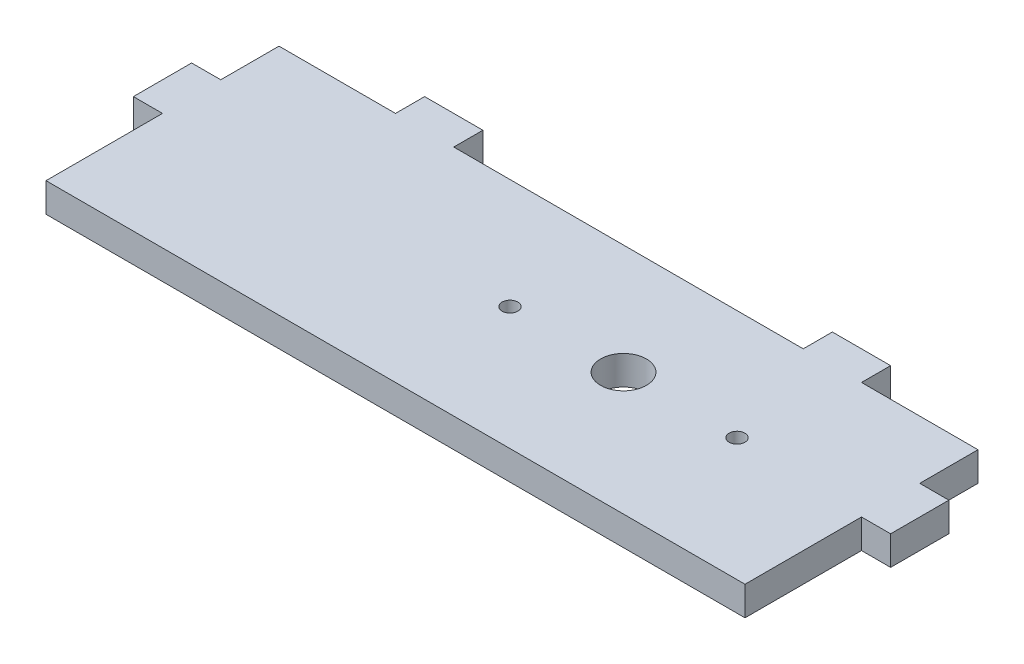
SolidWorks part; units mm, degrees
material "Beech"
ref_plane "Front Plane" through (0, 0, 0) normal (0, 0, 1) x (1, 0, 0)
ref_plane "Top Plane" through (0, 0, 0) normal (0, 1, 0) x (1, 0, 0)
ref_plane "Right Plane" through (0, 0, 0) normal (1, 0, 0) x (0, 0, -1)
sketch "Sketch1" plane through (0, 0, 0) normal (0, 1, 0) x (1, 0, 0)
  line L0 (0, 0) -> (0, 50.8)
  line L1 (0, 0) -> (152.4, 0)
  line L2 (0, 50.8) -> (152.4, 50.8)
  line L3 (152.4, 0) -> (152.4, 50.8)
  line L4 (0, 38.1) -> (-6.35, 38.1)
  line L5 (0, 38.1) -> (0, 25.4)
  line L6 (-6.35, 38.1) -> (-6.35, 25.4)
  line L7 (0, 25.4) -> (-6.35, 25.4)
  line L8 (25.4, 50.8) -> (25.4, 57.15)
  line L9 (25.4, 50.8) -> (38.1, 50.8)
  line L10 (25.4, 57.15) -> (38.1, 57.15)
  line L11 (38.1, 50.8) -> (38.1, 57.15)
  line L12 (114.3, 50.8) -> (114.3, 57.15)
  line L13 (114.3, 50.8) -> (127, 50.8)
  line L14 (114.3, 57.15) -> (127, 57.15)
  line L15 (127, 50.8) -> (127, 57.15)
  line L16 (152.4, 38.1) -> (158.75, 38.1)
  line L17 (152.4, 38.1) -> (152.4, 25.4)
  line L18 (158.75, 38.1) -> (158.75, 25.4)
  line L19 (152.4, 25.4) -> (158.75, 25.4)
  circle A0 centre (99.11, 26.8) radius 5
  circle A1 centre (123.86, 26.8) radius 1.725
  circle A2 centre (74.36, 26.8) radius 1.725
  point P27 (76.2, 50.8)
  dimension "D8" = 10
  dimension "D9" = 3.45
  dimension "D1" = 152.4
  dimension "D2" = 50.8
  dimension "D3" = 12.7
  dimension "D4" = 6.35
  dimension "D5" = 25.4
  dimension "D6" = 25.4
  dimension "D7" = 12.7
  dimension "D10" = 24.75
  dimension "D11" = 24.75
  dimension "D12" = 24
  dimension "D13" = 22.91
extrude "Boss-Extrude1" add sketch "Sketch1" along normal blind 6.35 contours L1 L3 L2 L0 A2 A1 A0 | L2 L11 L10 L8 | L7 L0 L4 L6 | L3 L19 L18 L16 | L2 L15 L14 L12
equation "\"CageLeftBottomEdge\"=22.11mm"
equation "\"CageLeftTopEdge\"=22.11mm"
equation "\"CageRightBottomEdge\"=21.63mm"
equation "\"CageRightTopEdge\"=21.63mm"
equation "\"CageHeight\"=86.04mm"
equation "\"CageLength\"=73.76mm"
equation "\"CageTopScrewClearance\"=10mm"
equation "\"CageBottomScrewClearance\"=25mm"
equation "\"CageLeftTopDepth\"= 11.65mm"
equation "\"CageLeftBottomDepth\"=11.11mm"
equation "\"CageLeftTopHeight\"=8.56175mm"
equation "\"CageLeftBottomHeight\"=16mm"
equation "\"CageRightTopDepth\"= 11.05mm"
equation "\"CageRightBottomDepth\"=10.58mm"
equation "\"CageRightTopHeight\"=9.6mm"
equation "\"CageRightBottomHeight\"=15.49mm"
equation "\"CageLeftTopChannelDepth\"=2.41908mm"
equation "\"CageLeftBottomChannelDepth\"=2.588mm"
equation "\"CageLeftChannelHeight\"=11.7mm"
equation "\"CageRightTopChannelDepth\"=2.32mm"
equation "\"CageRightBottomChannelDepth\"=2.318mm"
equation "\"CageRightChannelHeight\"=10mm"
equation "\"CageChanRelHeight\"=23.99mm"
equation "\"CageChanRelDepth\"=5.492mm"
equation "\"CageChamberRadius\"=16.261mm"
equation "\"CageScrewDiameter\"=4.8mm"
equation "\"CageSetScrewDiameter\"=3.5mm"
equation "\"CageAxleRadius\"=6.639mm"
equation "\"CageAxleKeyHeight\"=1.619mm"
equation "\"CageAxleKeyWidth\"=2.662mm"
equation "\"CageHoseWindowWidth\"=16.29mm"
equation "\"CageHoseWindowHeight\"=26.5mm"
equation "\"CageHoseWindow-Edge\"=8.89mm"
equation "\"CageScrew-VerticalEdge\"=5.0mm"
equation "\"CageScrew-HorizontalEdge\"=7.5mm"
equation "\"CageScrew-HoseCornerScrewEdge\"=4.45mm"
equation "\"CageAxle-BottomEdge\"=56.05mm"
equation "\"CageAxle-FrontEdge\"=46.03mm"
equation "\"CageBackSetScrew-Axle\"=40mm"
equation "\"CageFrontSetScrew-Axle\"=22mm"
equation "\"CageVelocityWindow-BackEdge\"=34.8mm"
equation "\"CageVelocityWindow-BottomEdge\"=27.55mm"
equation "\"CageVelocityWindowHeight\"=22.29mm"
equation "\"CageVelocityWindowWidth\"=12.61mm"
equation "\"TriggerSlot-BottomEdge\"=6.35mm"
equation "\"TriggerSlot-FrontEdge\"=15mm"
equation "\"TriggerSlotSize\"=6.7mm"
equation "\"TriggerRackOffset\"=.236224in"
equation "\"TriggerSlotSizeInt\"=.25in"
equation "\"MotorMountLegLength\"=.25in"
equation "\"GearOffset\"=.264907in"
equation "\"TriggerSlotSpacing\"=.25in"
equation "\"TriggerMiniSlotWidth\"=3.5mm"
equation "\"TriggerRackWidth\"=6.5mm"
equation "\"TGMGearFaceDiameter\"=24.40mm"
equation "\"TGMCylinderLength\"=15.00mm"
equation "\"TGMScrewHole-Center\"=8.70mm"
equation "\"TGMScrewHoleDiameter\"=5.04mm"
equation "\"TGMCenterHoleDiameter\"=9.50mm"
equation "\"TGMShaftCollarSideLength\"=19.00mm"
equation "\"TGMShaftCollarDockingDepth\"=7.00mm"
equation "\"whitemotordepth\"=11.27mm"
equation "\"whitemotorbackdepth\"=3.845mm"
equation "\"whitemotoraxledepth\" = 3.5mm"
equation "\"whitemotoraxleoffset\"=11.4mm"
equation "\"whitemotorwidth\"=12.07mm"
equation "\"whitemotorheight\"=16.68mm"
equation "\"whitemotorcylinderlength\" =13.04mm"
equation "\"whitemotorcylinderradius\"=3.845mm"
equation "\"whitemotorcylinderoffset\"=2.35mm"
equation "\"whitemotorcutoutlength\"=1.88mm"
equation "\"whitemotorouterrad\"=5mm"
equation "\"whitemotorinnerrad\"=2.95mm"
equation "\"elasticracklength\"=2in"
equation "\"elasticrackpegsize\"=.25in"
equation "\"elasticrackpegbuffer\"=.125in"
equation "\"elasticrackpegspacing\"=1.76476378in"
equation "\"elasticbaybuffer\"=.25in"
equation "\"elasticdepth\"=.125in"
equation "\"elasticbaydepth\"=.75in"
equation "\"motormountwidth\"=12mm"
equation "\"motormountcornerfillet\"=3mm"
equation "\"pandiscradius\"=14in"
equation "\"towermaterialwidth\"=.25in"
equation "\"towerslotlength\"=.5in"
equation "\"towermarkerspace\"=5in"
equation "\"towerslothorizoffset\"=1in"
equation "\"towerslothorizspacing\"=2in"
equation "\"towerslotvertoffset\"=3in"
equation "\"towerslotvertspacing\"=1in"
equation "\"towerheight\"=12in"
equation "\"towerupslot\"=1in"
equation "\"toweraxle\"=.5in"
equation "\"towerplatslotoffset\"=1.5in"
equation "\"towermotorpanelheight\"=10in"
equation "\"D1@Sketch1\"=(\"towerslothorizspacing\"+\"towerslothorizoffset\")*2"
equation "\"towerplatdepth\"=2in"
equation "\"D2@Sketch1\"=\"towerplatdepth\""
equation "\"D3@Sketch1\"=\"towerslotlength\""
equation "\"D4@Sketch1\"=\"towermaterialwidth\""
equation "\"D5@Sketch1\"=\"towerplatslotoffset\"-\"towerslotlength\""
equation "\"D6@Sketch1\"=\"towerplatslotoffset\"-\"towerslotlength\""
equation "\"D7@Sketch1\"=\"towerslotlength\""
equation "\"stepperouterrad\"=10mm"
equation "\"D8@Sketch1\"=\"stepperouterrad\""
equation "\"stepperscrewsize\"=3.45mm"
equation "\"D9@Sketch1\"=\"stepperscrewsize\""
equation "\"stepperscrewc2c\"=49.5mm"
equation "\"D10@Sketch1\"=\"stepperscrewc2c\"/2"
equation "\"D11@Sketch1\"=\"stepperscrewc2c\"/2"
equation "\"stepperdepthoffset\"=24mm"
equation "\"D12@Sketch1\"=\"stepperdepthoffset\""
equation "\"stepperhorizoffset\"=22.91mm"
equation "\"D13@Sketch1\"=\"stepperhorizoffset\""
equation "\"D1@Boss-Extrude1\"=\"towermaterialwidth\""
equation "\"shaftslotOD\"=18.8mm"
equation "\"shaftslotID\"=13.28mm"
equation "\"shaftkeywidth\"=2.67mm"
equation "\"shaftkeydepth\"=1.8mm"
equation "\"shaftcollartotaldepth\"=12.5mm"
equation "\"shaftsquaredepth\"=6mm"
equation "\"shaftsetscrewsize\"=3.5mm"
equation "\"shaftkeytightdepth\"=1.85mm"
equation "\"shaftslottightID\"=12.78mm"
equation "\"shaftsetscrewoffset\"=9mm"
equation "\"cagecollartotaldepth\"=10mm"
equation "\"cagecollartotalwidth\"=35mm"
equation "\"cagecollarbasedepth\"=4mm"
equation "\"ajaxaxlesize\"=3.87mm"
equation "\"ajaxinnercut\"=2.3mm"
equation "\"ajaxwidth\"=6.1mm"
equation "\"ajaxdiametral\"=25.8854"
equation "\"ajax4020gap\"=29.5mm"
equation "\"ajax4010gap\"=24.5mm"
equation "\"ajaxhubdepth\"=.25in"
equation "\"ajaxcutoutdepth\"=2.3mm"
equation "\"ajax20hubbuffer\"=0.240157in"
equation "\"ajax20hubholeoffset\"=.19685in"
equation "\"ajax20hubholesize\"=.059055in"
equation "\"ajax20cutoutint\"=13.4mm"
equation "\"ajax40hubholesize\"=7.21mm"
equation "\"ajax40hubholeoffset\"=10mm"
equation "\"ajax40hubbuffer\"=.350394in"
equation "\"ajax40cutoutint\"=32.6mm"
equation "\"no6diam\"=.146in"
equation "\"shconangle\"=20deg"
equation "\"shconlen\"=1in"
equation "\"lnconlen\"=1.5in"
equation "\"lnconangle\"=15deg"
